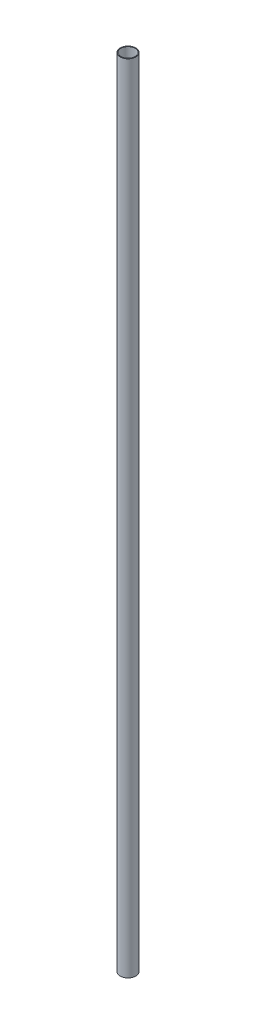
SolidWorks part; units mm, degrees
material "Thornel Mat VMA"
ref_plane "Front Plane" through (0, 0, 0) normal (0, 0, 1) x (1, 0, 0)
ref_plane "Top Plane" through (0, 0, 0) normal (0, 1, 0) x (1, 0, 0)
ref_plane "Right Plane" through (0, 0, 0) normal (1, 0, 0) x (0, 0, -1)
sketch "Sketch1" plane through (0, 0, 0) normal (0, 1, 0) x (1, 0, 0)
  circle A0 centre (0, 0) radius 10.541
  circle A1 centre (0, 0) radius 9.525
  dimension "D1" = 1.016
  dimension "D2" = 19.05
extrude "Boss-Extrude1" add sketch "Sketch1" along normal blind 1066.8
sketch3d "3DSketch1" plane through (0, 0, 0) normal (0, 0, 1) x (1, 0, 0)
  dimension "D1" = 355.6
